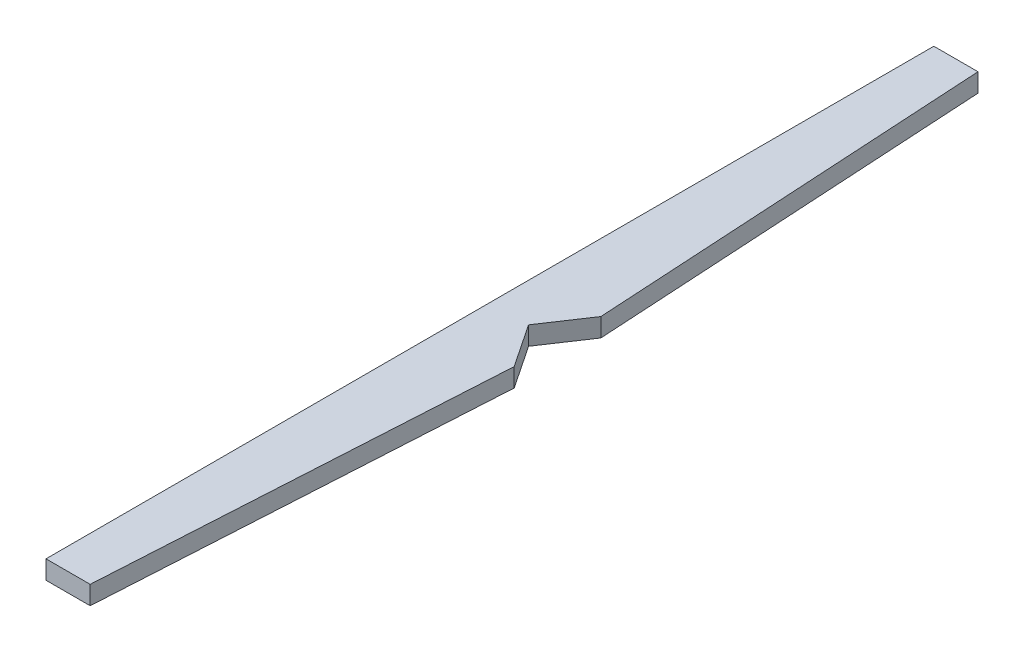
SolidWorks part; units mm, degrees
ref_plane "Front Plane" through (0, 0, 0) normal (0, 0, 1) x (1, 0, 0)
ref_plane "Top Plane" through (0, 0, 0) normal (0, 1, 0) x (1, 0, 0)
ref_plane "Right Plane" through (0, 0, 0) normal (1, 0, 0) x (0, 0, -1)
sketch "Sketch1" plane through (0, 0, 0) normal (0, 1, 0) x (1, 0, 0)
  line L0 (0, 497.2644) -> (0, -497.2644) construction
  line L1 (0, 358.35) -> (0, -358.35)
  line L2 (0, -358.35) -> (35.6506, -358.35)
  line L3 (35.6506, -358.35) -> (54.5725, -34.9979)
  line L4 (54.5725, 34.9979) -> (35.6506, 358.35)
  line L5 (35.6506, 358.35) -> (0, 358.35)
  line L6 (47.8, 150.7317) -> (0, 150.7317) construction
  line L7 (56.6205, 0) -> (723.1311, 0) construction
  line L8 (54.5725, 34.9979) -> (31.1966, 0)
  line L9 (31.1966, 0) -> (54.5725, -34.9979)
  point P4 (0, 0)
  point P7 (0, 0)
  dimension "D1" = 716.7
  dimension "D2" = 47.8
extrude "Boss-Extrude1" add sketch "Sketch1" along normal blind 15
